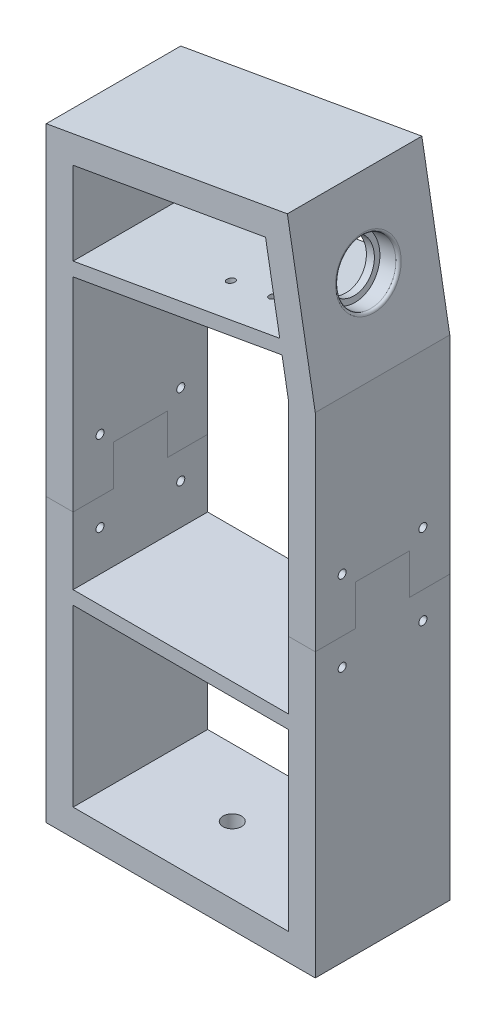
SolidWorks part; units mm, degrees
ref_plane "Front Plane" through (0, 0, 0) normal (0, 0, 1) x (1, 0, 0)
ref_plane "Top Plane" through (0, 0, 0) normal (0, 1, 0) x (1, 0, 0)
ref_plane "Right Plane" through (0, 0, 0) normal (1, 0, 0) x (0, 0, -1)
sketch "Sketch2" plane through (0, 0, 0) normal (0, 0, 1) x (1, 0, 0)
  line L6 (-50, 225.01) -> (-50, 0)
  line L8 (-50, 0) -> (50, 0)
  line L10 (-40, 216.619) -> (-40, 10)
  line L11 (-40, 10) -> (40, 10)
  line L12 (50, 0) -> (50, 182.01)
  line L13 (50, 182.01) -> (39.6312, 240.8144)
  line L14 (50, 182.01) -> (50, 266.0824) construction
  line L15 (39.6312, 240.8144) -> (-50, 225.01)
  line L16 (40, 10) -> (40, 181.1351)
  line L17 (40, 181.1351) -> (31.5196, 229.2298)
  line L18 (31.5196, 229.2298) -> (-40, 216.619)
  dimension "D1" = 182.01
  dimension "D2" = 100
  dimension "D3" = 10
  dimension "D4" = 225.01
  dimension "D6" = 10
extrude "Boss-Extrude1" add sketch "Sketch2" along normal blind 50
sketch "Sketch4" plane through (79.6179, 14.0388, 0) normal (0.9848, 0.1736, 0) x (0, 0, -1)
  line L0 (-25, 170.5625) -> (-25, 200.891) construction
  line L1 (-50, 170.5625) -> (0, 170.5625) construction
  line L2 (-50, 230.274) -> (0, 230.274) construction
  circle A0 centre (-25, 200.891) radius 11.025
  dimension "D1" = 22.05
  dimension "D2" = 29.383
extrude "Cut-Extrude1" cut sketch "Sketch4" against normal blind 7
sketch "Sketch5" plane through (72.7242, 12.8232, 0) normal (0.9848, 0.1736, 0) x (0, 0, -1)
  line L0 (-25, 211.916) -> (-25, 189.866) construction
  circle A0 centre (-25, 200.891) radius 11.025 construction
  circle A1 centre (-25, 200.891) radius 11.025 construction
  circle A2 centre (-25, 200.891) radius 9
  dimension "D1" = 18
extrude "Cut-Extrude2" cut sketch "Sketch5" against normal blind 7
sketch "Sketch7" plane through (0, 0, 50) normal (0, 0, 1) x (1, 0, 0)
  line L0 (40, 181.1351) -> (31.5196, 229.2298) construction
  line L5 (36.795, 199.3114) -> (37.6633, 194.3873)
  line L7 (-40, 180.6932) -> (-40, 185.7703)
  line L10 (36.795, 199.3114) -> (-40, 185.7703)
  line L11 (-40, 180.6932) -> (37.6633, 194.3873)
  line L12 (-40, 216.619) -> (-40, 10) construction
  line L13 (31.5196, 229.2298) -> (-40, 216.619) construction
  dimension "D1" = 30.38
  dimension "D3" = 5
extrude "Boss-Extrude2" add sketch "Sketch7" against normal blind 50
sketch "Sketch8" plane through (-50, 0, 0) normal (-1, 0, 0) x (0, 0, 1)
  line L0 (50, 225.01) -> (0, 225.01) construction
  line L1 (50, 225.01) -> (50, 0) construction
  line L3 (0, 225.01) -> (0, 0) construction
  line L4 (0, 204.1639) -> (50, 204.1639) construction
  circle A0 centre (25, 204.1639) radius 5
  dimension "D1" = 10
  dimension "D2" = 20.8461
extrude "Cut-Extrude3" cut sketch "Sketch8" against normal blind 10
sketch "Sketch9" plane through (123.2339, 209.4758, 0) normal (-0.1736, 0.9848, 0) x (-0.9848, -0.1736, 0)
  line L0 (76.8907, 25) -> (104.9692, 25) construction
  line L3 (104.9692, 34.6) -> (120.9692, 34.6) construction
  line L5 (76.8907, 50) -> (76.8907, 0) construction
  line L6 (104.9692, 25) -> (104.9692, 34.6) construction
  line L7 (104.9692, 25) -> (104.9692, 15.4) construction
  line L8 (120.9692, 34.6) -> (120.9692, 15.4) construction
  line L10 (120.9692, 15.4) -> (104.9692, 15.4) construction
  circle A0 centre (104.9692, 15.4) radius 1.485
  circle A1 centre (104.9692, 34.6) radius 1.485
  circle A2 centre (120.9692, 34.6) radius 1.485
  circle A3 centre (120.9692, 15.4) radius 1.485
  dimension "D1" = 28.0785
  dimension "D2" = 2.97
  dimension "D3" = 19.2
  dimension "D4" = 16
extrude "Cut-Extrude4" cut sketch "Sketch9" along normal up to next contours A3
sketch "Sketch10" plane through (0, 10, 0) normal (0, 1, 0) x (1, 0, 0)
  line L0 (50, -25) -> (24.131, -25) construction
  line L1 (-30.869, -50) -> (-30.869, 0) construction
  line L2 (50, -50) -> (50, 0) construction
  line L3 (-30, -25) -> (-5.8513, -25) construction
  circle A0 centre (-5.8513, -25) radius 3.425
  circle A1 centre (24.131, -25) radius 3.425
  dimension "D1" = 6.85
  dimension "D2" = 6.85
  dimension "D3" = 25.0177
  dimension "D4" = 55
extrude "Cut-Extrude5" cut sketch "Sketch10" against normal blind 10
sketch "Sketch11" plane through (0, 0, 50) normal (0, 0, 1) x (1, 0, 0)
  line L0 (-40, 75) -> (40, 75)
  line L3 (40, 75) -> (40, 80)
  line L4 (40, 80) -> (-40, 80)
  line L5 (-40, 80) -> (-40, 75)
  line L6 (-40, 180.6932) -> (-40, 10) construction
  line L7 (40, 10) -> (40, 181.1351) construction
  dimension "D1" = 5
  dimension "D2" = 75
extrude "Boss-Extrude3" add sketch "Sketch11" against normal blind 50
fillet "Fillet1" radius 1 1 edges at (42.819, 222.7353, 25)
sketch "Sketch14" plane through (-50, 0, 0) normal (-1, 0, 0) x (0, 0, 1)
  line L0 (0, 0) -> (0, 105) construction
  line L1 (0, 225.01) -> (0, 0) construction
  line L2 (0, 105) -> (50, 105) construction
  line L3 (50, 225.01) -> (50, 0) construction
  line L4 (50, 105) -> (50, 125) construction
  line L5 (50, 105) -> (50, 95) construction
  line L6 (50, 125) -> (40, 125) construction
  line L7 (50, 95) -> (40, 95) construction
  line L8 (25, 0) -> (25, 105) construction
  line L10 (50, 0) -> (0, 0) construction
  circle A0 centre (40, 125) radius 1.5
  circle A1 centre (40, 95) radius 1.5
  circle A2 centre (10, 95) radius 1.5
  circle A3 centre (10, 125) radius 1.5
  dimension "D1" = 3
  dimension "D2" = 3
  dimension "D3" = 95
  dimension "D4" = 125
  dimension "D5" = 15
extrude "Cut-Extrude6" cut sketch "Sketch14" against normal through all
sketch "Sketch15" plane through (-50, 0, 0) normal (-1, 0, 0) x (0, 0, 1)
  line L0 (0, 0) -> (0, 105) construction
  line L1 (0, 225.01) -> (0, 0) construction
  line L2 (0, 105) -> (15, 105)
  line L3 (15, 105) -> (15, 120)
  line L4 (15, 120) -> (35, 120)
  line L5 (35, 120) -> (35, 105)
  line L6 (35, 105) -> (50, 105)
  line L7 (50, 225.01) -> (50, 0) construction
  line L8 (50, 0) -> (0, 0) construction
  dimension "D1" = 15
  dimension "D2" = 35
  dimension "D3" = 15
  dimension "D4" = 105
  dimension "D5" = 105
split "Split1" trim tools "Sketch15" bodies to split 116 resulting bodies 117 118
